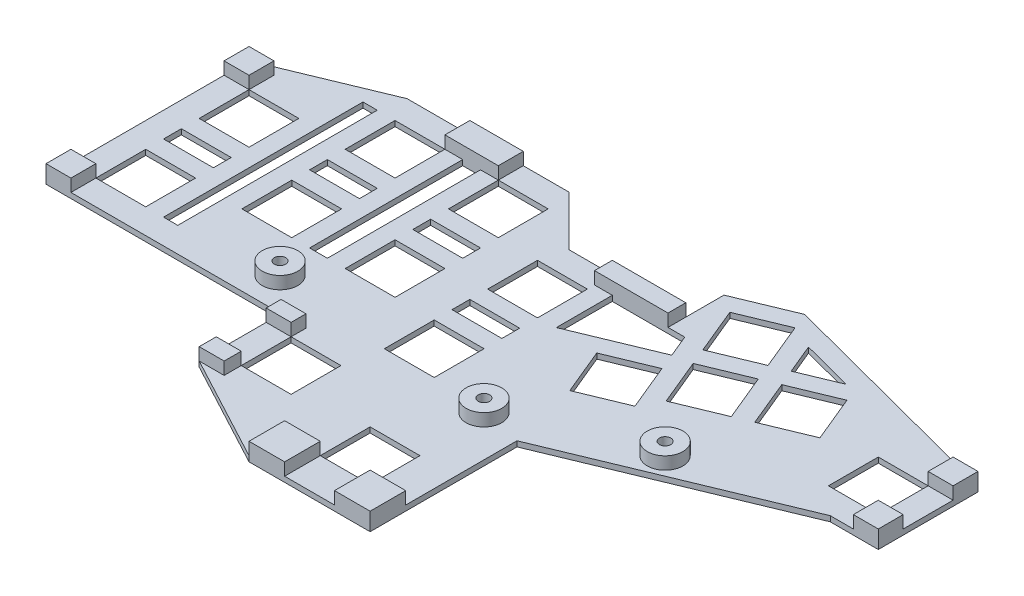
SolidWorks part; units mm, degrees
ref_plane "Front Plane" through (0, 0, 0) normal (0, 0, 1) x (1, 0, 0)
ref_plane "Top Plane" through (0, 0, 0) normal (0, 1, 0) x (1, 0, 0)
ref_plane "Right Plane" through (0, 0, 0) normal (1, 0, 0) x (0, 0, -1)
sketch "Button Reference" plane through (0, 0, 0) normal (0, 1, 0) x (1, 0, 0)
  line L0 (-8.4377, 29.6405) -> (9.1622, 36.9307) construction
  line L1 (-8.4377, 29.6405) -> (-15.7278, 47.2404) construction
  line L2 (9.1622, 36.9307) -> (7.6315, 40.6262) construction
  line L3 (-15.7278, 47.2404) -> (1.8721, 54.5306) construction
  line L4 (-8.4377, 29.6405) -> (1.8721, 54.5306) construction
  line L5 (9.1622, 36.9307) -> (-15.7278, 47.2404) construction
  line L6 (7.6315, 40.6262) -> (25.2314, 47.9163) construction
  line L7 (1.8721, 54.5306) -> (0.3413, 58.2261) construction
  line L8 (25.2314, 47.9163) -> (17.9412, 65.5162) construction
  line L9 (0.3413, 58.2261) -> (17.9412, 65.5162) construction
  line L10 (7.6315, 40.6262) -> (17.9412, 65.5162) construction
  line L11 (25.2314, 47.9163) -> (0.3413, 58.2261) construction
  line L12 (25.2314, 47.9163) -> (42.8313, 55.2064) construction
  line L13 (42.8313, 55.2064) -> (35.5411, 72.8063) construction
  line L14 (17.9412, 65.5162) -> (35.5411, 72.8063) construction
  line L15 (25.2314, 47.9163) -> (35.5411, 72.8063) construction
  line L16 (42.8313, 55.2064) -> (17.9412, 65.5162) construction
  line L17 (17.9412, 65.5162) -> (10.6511, 83.1161) construction
  line L18 (0.3413, 58.2261) -> (-6.9488, 75.826) construction
  line L19 (10.6511, 83.1161) -> (-6.9488, 75.826) construction
  line L20 (17.9412, 65.5162) -> (-6.9488, 75.826) construction
  line L21 (0.3413, 58.2261) -> (10.6511, 83.1161) construction
  line L22 (25.6906, 46.8076) -> (43.2905, 54.0978)
  line L23 (43.9399, 55.6656) -> (36.6498, 73.2655)
  line L24 (18.5907, 67.0841) -> (35.0819, 73.915)
  line L25 (18.5907, 67.0841) -> (11.7598, 83.5753)
  line L26 (10.1919, 84.2248) -> (-7.408, 76.9346)
  line L27 (-0.7673, 57.7669) -> (-8.0574, 75.3668)
  line L28 (0.3042, 55.18) -> (-0.7673, 57.7669)
  line L29 (-16.1871, 48.3491) -> (0.3042, 55.18)
  line L30 (-9.5464, 29.1813) -> (-16.8365, 46.7812)
  line L31 (-7.9785, 28.5319) -> (9.6214, 35.822)
  line L32 (10.2708, 37.3899) -> (9.1993, 39.9767)
  line L33 (9.1993, 39.9767) -> (25.6906, 46.8076)
  line L34 (-130.2828, 54.0855) -> (-140.7133, 54.0855) construction
  line L35 (-36.2828, 53.0855) -> (-36.2828, 24.0855) construction
  line L36 (-61.2828, 67.0855) -> (-61.2828, 38.0855) construction
  line L37 (-90.2828, 67.0855) -> (-90.2828, 38.0855) construction
  line L38 (-118.2828, 54.0855) -> (-118.2828, 25.0855) construction
  line L39 (71.3862, 53.0939) -> (81.8167, 53.0939) construction
  line L40 (-36.2828, -4.9145) -> (-36.2828, 24.0855) construction
  line L41 (-36.2828, 24.0855) -> (-52.2828, -0.1012) construction
  line L42 (-36.2828, 53.0855) -> (-3.2828, 42.0855) construction
  line L43 (30.3862, 60.3613) -> (59.3862, 53.0939) construction
  circle A0 centre (59.3862, 53.0939) radius 12
  circle A1 centre (-36.2828, 24.0855) radius 12
  circle A2 centre (-61.2828, 38.0855) radius 12
  circle A3 centre (-90.2828, 38.0855) radius 12
  circle A4 centre (-90.2828, 67.0855) radius 12
  circle A5 centre (-61.2828, 67.0855) radius 12
  circle A6 centre (-36.2828, 53.0855) radius 12
  arc A7 (-7.408, 76.9346) -> (-8.0574, 75.3668) centre (-6.9488, 75.826) ccw
  arc A8 (-16.1871, 48.3491) -> (-16.8365, 46.7812) centre (-15.7278, 47.2404) ccw
  arc A9 (-9.5464, 29.1813) -> (-7.9785, 28.5319) centre (-8.4377, 29.6405) ccw
  arc A10 (9.6214, 35.822) -> (10.2708, 37.3899) centre (9.1622, 36.9307) ccw
  arc A11 (43.2905, 54.0978) -> (43.9399, 55.6656) centre (42.8313, 55.2064) ccw
  arc A12 (11.7598, 83.5753) -> (10.1919, 84.2248) centre (10.6511, 83.1161) ccw
  arc A13 (36.6498, 73.2655) -> (35.0819, 73.915) centre (35.5411, 72.8063) ccw
  circle A14 centre (-118.2828, 54.0855) radius 12
  circle A15 centre (-118.2828, 25.0855) radius 12
  circle A16 centre (-19.2828, -10.9145) radius 15
  circle A17 centre (-52.2828, -0.1012) radius 12
  point P25 (-3.2828, 42.0855)
  point P26 (12.7863, 53.0712)
  point P27 (30.3862, 60.3613)
  point P32 (5.4962, 70.6711)
  dimension "D1" = 24
  dimension "D2" = 24
  dimension "D4" = 1.2
  dimension "D17" = 30
  dimension "D3" = 19.05
  dimension "D5" = 7.2675
  dimension "D6" = 4
  dimension "D7" = 25
  dimension "D8" = 29
  dimension "D9" = 14
  dimension "D10" = 29
  dimension "D11" = 13
  dimension "D12" = 28
  dimension "D13" = 18
  dimension "D14" = 33
  dimension "D15" = 53
  dimension "D16" = 16
  dimension "D18" = 29
  dimension "D19" = 16
sketch "Sketch2" plane through (0, 0, 0) normal (0, 1, 0) x (1, 0, 0)
  line L0 (5.8631, 38.2972) -> (-7.0712, 32.9396)
  line L1 (-125.2828, 61.0855) -> (-111.2828, 61.0855)
  line L2 (-125.2828, 61.0855) -> (-125.2828, 47.0855)
  line L3 (-125.2828, 47.0855) -> (-111.2828, 47.0855)
  line L4 (-111.2828, 61.0855) -> (-111.2828, 47.0855)
  line L5 (-125.2828, 61.0855) -> (-111.2828, 47.0855) construction
  line L6 (-125.2828, 47.0855) -> (-111.2828, 61.0855) construction
  line L7 (-97.2828, 74.0855) -> (-83.2828, 74.0855)
  line L8 (-97.2828, 74.0855) -> (-97.2828, 60.0855)
  line L9 (-97.2828, 60.0855) -> (-83.2828, 60.0855)
  line L10 (-83.2828, 74.0855) -> (-83.2828, 60.0855)
  line L11 (-97.2828, 74.0855) -> (-83.2828, 60.0855) construction
  line L12 (-97.2828, 60.0855) -> (-83.2828, 74.0855) construction
  line L13 (-68.2828, 74.0855) -> (-54.2828, 74.0855)
  line L14 (-68.2828, 74.0855) -> (-68.2828, 60.0855)
  line L15 (-68.2828, 60.0855) -> (-54.2828, 60.0855)
  line L16 (-54.2828, 74.0855) -> (-54.2828, 60.0855)
  line L17 (-68.2828, 74.0855) -> (-54.2828, 60.0855) construction
  line L18 (-68.2828, 60.0855) -> (-54.2828, 74.0855) construction
  line L19 (-43.2828, 46.0855) -> (-29.2828, 46.0855)
  line L20 (-43.2828, 46.0855) -> (-43.2828, 60.0855)
  line L21 (-43.2828, 60.0855) -> (-29.2828, 60.0855)
  line L22 (-29.2828, 46.0855) -> (-29.2828, 60.0855)
  line L23 (-43.2828, 46.0855) -> (-29.2828, 60.0855) construction
  line L24 (-43.2828, 60.0855) -> (-29.2828, 46.0855) construction
  line L25 (-68.2828, 45.0855) -> (-54.2828, 45.0855)
  line L26 (-68.2828, 45.0855) -> (-68.2828, 31.0855)
  line L27 (-68.2828, 31.0855) -> (-54.2828, 31.0855)
  line L28 (-54.2828, 45.0855) -> (-54.2828, 31.0855)
  line L29 (-68.2828, 45.0855) -> (-54.2828, 31.0855) construction
  line L30 (-68.2828, 31.0855) -> (-54.2828, 45.0855) construction
  line L31 (-97.2828, 45.0855) -> (-83.2828, 45.0855)
  line L32 (-97.2828, 45.0855) -> (-97.2828, 31.0855)
  line L33 (-97.2828, 31.0855) -> (-83.2828, 31.0855)
  line L34 (-83.2828, 45.0855) -> (-83.2828, 31.0855)
  line L35 (-97.2828, 45.0855) -> (-83.2828, 31.0855) construction
  line L36 (-97.2828, 31.0855) -> (-83.2828, 45.0855) construction
  line L37 (-125.2828, 32.0855) -> (-111.2828, 32.0855)
  line L38 (-125.2828, 32.0855) -> (-125.2828, 18.0855)
  line L39 (-125.2828, 18.0855) -> (-111.2828, 18.0855)
  line L40 (-111.2828, 32.0855) -> (-111.2828, 18.0855)
  line L41 (-125.2828, 32.0855) -> (-111.2828, 18.0855) construction
  line L42 (-125.2828, 18.0855) -> (-111.2828, 32.0855) construction
  line L43 (-59.2828, 6.8988) -> (-45.2828, 6.8988)
  line L44 (-59.2828, 6.8988) -> (-59.2828, -7.1012)
  line L45 (-59.2828, -7.1012) -> (-45.2828, -7.1012)
  line L46 (-45.2828, 6.8988) -> (-45.2828, -7.1012)
  line L47 (-59.2828, 6.8988) -> (-45.2828, -7.1012) construction
  line L48 (-59.2828, -7.1012) -> (-45.2828, 6.8988) construction
  line L49 (-43.2828, 17.0855) -> (-29.2828, 17.0855)
  line L50 (-43.2828, 17.0855) -> (-43.2828, 31.0855)
  line L51 (-43.2828, 31.0855) -> (-29.2828, 31.0855)
  line L52 (-29.2828, 17.0855) -> (-29.2828, 31.0855)
  line L53 (-43.2828, 17.0855) -> (-29.2828, 31.0855) construction
  line L54 (-43.2828, 31.0855) -> (-29.2828, 17.0855) construction
  line L55 (-26.2828, -3.9145) -> (-12.2828, -3.9145)
  line L56 (-26.2828, -3.9145) -> (-26.2828, -17.9145)
  line L57 (-26.2828, -17.9145) -> (-12.2828, -17.9145)
  line L58 (-12.2828, -3.9145) -> (-12.2828, -17.9145)
  line L59 (-26.2828, -3.9145) -> (-12.2828, -17.9145) construction
  line L60 (-26.2828, -17.9145) -> (-12.2828, -3.9145) construction
  line L61 (52.3862, 60.0939) -> (66.3862, 60.0939)
  line L62 (52.3862, 60.0939) -> (52.3862, 46.0939)
  line L63 (52.3862, 46.0939) -> (66.3862, 46.0939)
  line L64 (66.3862, 60.0939) -> (66.3862, 46.0939)
  line L65 (52.3862, 60.0939) -> (66.3862, 46.0939) construction
  line L66 (52.3862, 46.0939) -> (66.3862, 60.0939) construction
  line L67 (5.8631, 38.2972) -> (0.5055, 51.2315)
  line L68 (-7.0712, 32.9396) -> (-12.4288, 45.8739)
  line L69 (0.5055, 51.2315) -> (-12.4288, 45.8739)
  line L70 (5.8631, 38.2972) -> (-12.4288, 45.8739) construction
  line L71 (-7.0712, 32.9396) -> (0.5055, 51.2315) construction
  line L72 (-3.6497, 74.4595) -> (9.2846, 79.817)
  line L73 (-3.6497, 74.4595) -> (1.7079, 61.5251)
  line L74 (9.2846, 79.817) -> (14.6422, 66.8827)
  line L75 (1.7079, 61.5251) -> (14.6422, 66.8827)
  line L76 (-3.6497, 74.4595) -> (14.6422, 66.8827) construction
  line L77 (9.2846, 79.817) -> (1.7079, 61.5251) construction
  line L78 (3.6404, 56.8596) -> (16.5747, 62.2171)
  line L79 (3.6404, 56.8596) -> (8.998, 43.9252)
  line L80 (16.5747, 62.2171) -> (21.9323, 49.2828)
  line L81 (8.998, 43.9252) -> (21.9323, 49.2828)
  line L82 (3.6404, 56.8596) -> (21.9323, 49.2828) construction
  line L83 (16.5747, 62.2171) -> (8.998, 43.9252) construction
  line L84 (26.5979, 51.2154) -> (39.5322, 56.5729)
  line L85 (26.5979, 51.2154) -> (21.2403, 64.1497)
  line L86 (39.5322, 56.5729) -> (34.1746, 69.5072)
  line L87 (21.2403, 64.1497) -> (34.1746, 69.5072)
  line L88 (26.5979, 51.2154) -> (34.1746, 69.5072) construction
  line L89 (39.5322, 56.5729) -> (21.2403, 64.1497) construction
  line L90 (10.1919, 84.2248) -> (-7.408, 76.9346) construction
  line L91 (-132.2828, 11.0855) -> (-132.2828, 68.0855)
  line L92 (-132.2828, 68.0855) -> (-100.8981, 81.0855)
  line L93 (-100.8981, 81.0855) -> (-55.4838, 81.0855)
  line L94 (-55.4838, 81.0855) -> (-41.4838, 67.0855)
  line L95 (-41.4838, 67.0855) -> (-8.6497, 67.0855)
  line L98 (7.3712, 84.4364) -> (73.3862, 67.0939)
  line L99 (73.3862, 67.0939) -> (73.3862, 39.0939)
  line L100 (73.3862, 39.0939) -> (59.9183, 39.0939)
  line L101 (59.9183, 39.0939) -> (-2.2828, 13.3293)
  line L102 (-2.2828, 13.3293) -> (-2.2828, -27.9145)
  line L103 (-2.2828, -27.9145) -> (-36.2828, -27.9145)
  line L104 (-36.2828, -27.9145) -> (-66.2828, -11.8979)
  line L105 (-66.2828, -11.8979) -> (-66.2828, 11.0855)
  line L108 (-66.2828, 11.0855) -> (-132.2828, 11.0855)
  line L109 (-8.6497, 67.0855) -> (-8.6497, 77.8004)
  line L110 (-8.6497, 77.8004) -> (7.3712, 84.4364)
  line L112 (-60.2893, -15.0978) -> (-57.9344, -10.687) construction
  line L113 (-24.2828, 62.0855) -> (-3.9362, 62.0855)
  line L114 (-102.2828, 74.0855) -> (-106.2828, 74.0855)
  line L115 (-102.2828, 74.0855) -> (-102.2828, 18.0855)
  line L116 (-102.2828, 18.0855) -> (-106.2828, 18.0855)
  line L117 (-106.2828, 74.0855) -> (-106.2828, 18.0855)
  line L118 (-73.2828, 74.0855) -> (-78.2828, 74.0855)
  line L119 (-73.2828, 74.0855) -> (-73.2828, 31.0855)
  line L120 (-73.2828, 31.0855) -> (-78.2828, 31.0855)
  line L121 (-78.2828, 74.0855) -> (-78.2828, 31.0855)
  line L122 (-97.2828, 55.0855) -> (-83.2828, 55.0855)
  line L123 (-97.2828, 55.0855) -> (-97.2828, 50.0855)
  line L124 (-97.2828, 50.0855) -> (-83.2828, 50.0855)
  line L125 (-83.2828, 55.0855) -> (-83.2828, 50.0855)
  line L126 (-68.2828, 55.0855) -> (-54.2828, 55.0855)
  line L127 (-68.2828, 55.0855) -> (-68.2828, 50.0855)
  line L128 (-68.2828, 50.0855) -> (-54.2828, 50.0855)
  line L129 (-54.2828, 55.0855) -> (-54.2828, 50.0855)
  line L130 (-43.2828, 41.0855) -> (-29.2828, 41.0855)
  line L131 (-43.2828, 41.0855) -> (-43.2828, 36.0855)
  line L132 (-43.2828, 36.0855) -> (-29.2828, 36.0855)
  line L133 (-29.2828, 41.0855) -> (-29.2828, 36.0855)
  line L138 (-125.2828, 42.0855) -> (-111.2828, 42.0855)
  line L139 (-125.2828, 42.0855) -> (-125.2828, 37.0855)
  line L140 (-125.2828, 37.0855) -> (-111.2828, 37.0855)
  line L141 (-111.2828, 42.0855) -> (-111.2828, 37.0855)
  line L142 (-3.9362, 62.0855) -> (-1.3617, 55.87)
  line L143 (-1.3617, 55.87) -> (-24.2828, 46.3758)
  line L145 (-24.2828, 46.3758) -> (-24.2828, 62.0855)
  line L146 (19.2807, 68.7499) -> (30.195, 73.2708)
  line L147 (30.195, 73.2708) -> (15.8468, 77.0402)
  line L148 (15.8468, 77.0402) -> (19.2807, 68.7499)
  circle A0 centre (-52.2828, -0.1012) radius 12 construction
  point P0 (-118.2828, 54.0855)
  point P6 (-90.2828, 67.0855)
  point P12 (-61.2828, 67.0855)
  point P18 (-36.2828, 53.0855)
  point P24 (-61.2828, 38.0855)
  point P30 (-90.2828, 38.0855)
  point P36 (-118.2828, 25.0855)
  point P42 (-52.2828, -0.1012)
  point P48 (-36.2828, 24.0855)
  point P54 (-19.2828, -10.9145)
  point P60 (59.3862, 53.0939)
  point P67 (-3.2828, 42.0855)
  point P68 (5.4962, 70.6711)
  point P69 (12.7863, 53.0712)
  point P74 (30.3862, 60.3613)
  dimension "D1" = 14
  dimension "D2" = 14
  dimension "D3" = 17
  dimension "D4" = 17
  dimension "D5" = 14
  dimension "D6" = 14
  dimension "D7" = 14
  dimension "D8" = 14
  dimension "D9" = 5
  dimension "D10" = 50
  dimension "D11" = 14
  dimension "D12" = 45
  dimension "D13" = 5
  dimension "D14" = 5
  dimension "D15" = 14
  dimension "D16" = 14
  dimension "D17" = 5
  dimension "D18" = 5
  dimension "D19" = 5
  dimension "D20" = 5
  dimension "D21" = 5
  dimension "D22" = 5
  dimension "D23" = 5
  dimension "D24" = 5
  dimension "D25" = 5
  dimension "D26" = 5
  dimension "D27" = 5
  dimension "D28" = 5
  dimension "D29" = 5
  dimension "D30" = 5
  dimension "D31" = 5
  dimension "D32" = 5
  dimension "D33" = 5
extrude "Key Plate" add sketch "Sketch2" along normal blind 1.5
sketch "Sketch4" plane through (0, 1.5, 0) normal (0, -1, 0) x (1, 0, 0)
  line L0 (-55.4838, -81.0855) -> (-100.8981, -81.0855) construction
  line L1 (-2.2828, 27.9145) -> (-12.2828, 27.9145)
  line L2 (-2.2828, 27.9145) -> (-2.2828, 17.9145)
  line L3 (-2.2828, 17.9145) -> (-12.2828, 17.9145)
  line L4 (-12.2828, 27.9145) -> (-12.2828, 17.9145)
  line L5 (73.3862, -39.0939) -> (66.3862, -39.0939)
  line L6 (73.3862, -39.0939) -> (73.3862, -46.0939)
  line L7 (73.3862, -46.0939) -> (66.3862, -46.0939)
  line L8 (66.3862, -39.0939) -> (66.3862, -46.0939)
  line L9 (73.3862, -67.0939) -> (66.3862, -67.0939)
  line L10 (73.3862, -67.0939) -> (73.3862, -60.0939)
  line L11 (73.3862, -60.0939) -> (66.3862, -60.0939)
  line L12 (66.3862, -67.0939) -> (66.3862, -60.0939)
  line L13 (-132.2828, -11.0855) -> (-125.2828, -11.0855)
  line L14 (-132.2828, -11.0855) -> (-132.2828, -18.0855)
  line L15 (-132.2828, -18.0855) -> (-125.2828, -18.0855)
  line L16 (-125.2828, -11.0855) -> (-125.2828, -18.0855)
  line L17 (-125.2828, -61.0855) -> (-132.2828, -61.0855)
  line L18 (-125.2828, -61.0855) -> (-125.2828, -68.0855)
  line L19 (-125.2828, -68.0855) -> (-132.2828, -68.0855)
  line L20 (-132.2828, -61.0855) -> (-132.2828, -68.0855)
  line L21 (-66.2828, 11.8979) -> (-59.2828, 11.8979)
  line L22 (-66.2828, 11.8979) -> (-66.2828, 7.1012)
  line L23 (-66.2828, 7.1012) -> (-59.2828, 7.1012)
  line L24 (-59.2828, 11.8979) -> (-59.2828, 7.1012)
  line L25 (-26.2828, 17.9145) -> (-36.2828, 17.9145)
  line L26 (-26.2828, 17.9145) -> (-26.2828, 27.9145)
  line L27 (-26.2828, 27.9145) -> (-36.2828, 27.9145)
  line L28 (-36.2828, 17.9145) -> (-36.2828, 27.9145)
  line L29 (-66.2828, -11.0855) -> (-59.2828, -11.0855)
  line L30 (-66.2828, -11.0855) -> (-66.2828, -6.8988)
  line L31 (-66.2828, -6.8988) -> (-59.2828, -6.8988)
  line L32 (-59.2828, -11.0855) -> (-59.2828, -6.8988)
  line L33 (-68.2828, -74.0855) -> (-83.2828, -74.0855)
  line L34 (-68.2828, -74.0855) -> (-68.2828, -81.0855)
  line L35 (-68.2828, -81.0855) -> (-83.2828, -81.0855)
  line L36 (-83.2828, -74.0855) -> (-83.2828, -81.0855)
  line L37 (-29.2828, -46.0855) -> (-29.2828, -60.0855) construction
  line L38 (-8.6497, -67.0855) -> (-29.2828, -67.0855)
  line L39 (-8.6497, -67.0855) -> (-8.6497, -62.0855)
  line L40 (-8.6497, -62.0855) -> (-29.2828, -62.0855)
  line L41 (-29.2828, -67.0855) -> (-29.2828, -62.0855)
  line L42 (-3.9362, -62.0855) -> (-24.2828, -62.0855) construction
  point P63 (-8.6497, -62.0855)
extrude "Standoffs" add sketch "Sketch4" against normal blind 3.5
sketch "Sketch6" plane through (0, 1.5, 0) normal (0, -1, 0) x (1, 0, 0)
  circle A0 centre (22.1408, -30.4875) radius 5
  circle A1 centre (-13.8038, -15.5645) radius 5
  circle A2 centre (-75.7828, -20.295) radius 5
extrude "Screw Guides" add sketch "Sketch6" against normal blind 3.5
hole_wizard "M3 Clearance Hole1" positions "3DSketch1" profile "Sketch7" hole size "M3" standard "ANSI Metric" end condition through all
sketch3d "3DSketch1"
  line L0 (22.1408, 5, -30.4875) -> (22.1408, 1.5, -30.4875) construction
  line L1 (-75.7828, 5, -20.295) -> (-75.7828, 1.5, -20.295) construction
  line L2 (-13.8038, 5, -15.5645) -> (-13.8038, 1.5, -15.5645) construction
  point P0 (22.1408, 5, -30.4875)
  point P4 (-75.7828, 5, -20.295)
  point P8 (-13.8038, 5, -15.5645)
sketch "Sketch7" plane through (22.1408, 5, -30.4875) normal (1, 0, 0) x (0, 0, 1)
  line L0 (0, 0) -> (0, 5)
  line L1 (0, 5) -> (1.6, 5)
  line L2 (1.6, 5) -> (1.6, 0)
  line L5 (1.6, 0) -> (0, 0)
  line L11 (0, -6.35) -> (0, 107.95) construction
  dimension "Thru Hole Dia." = 3.2
  dimension "Thru Hole Depth" = 5
